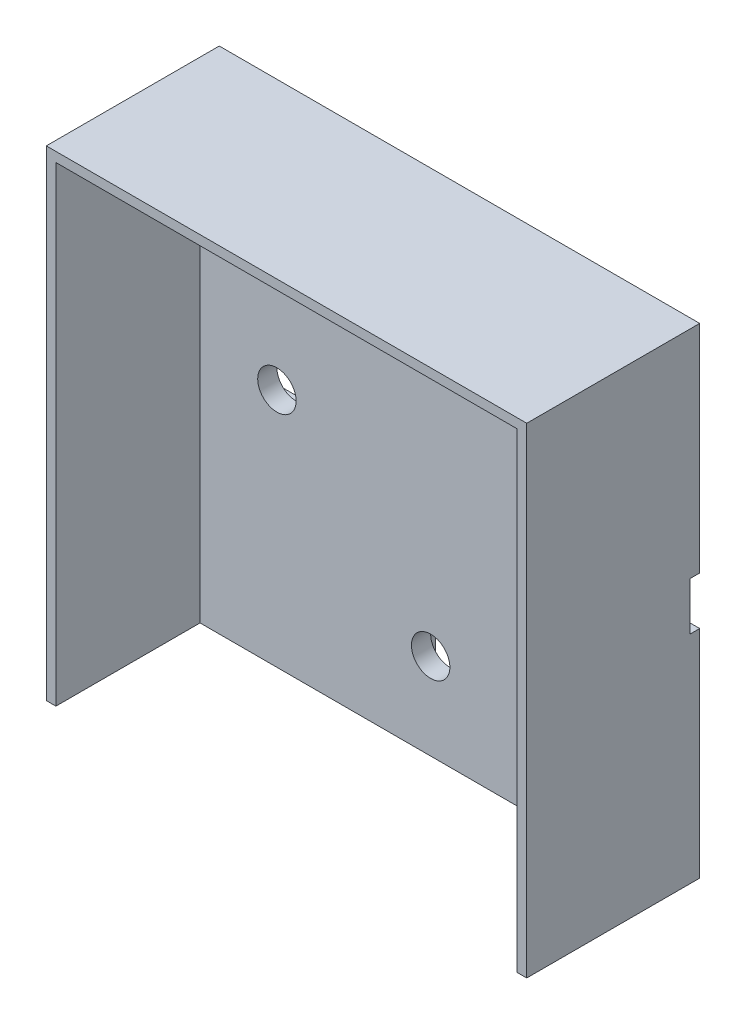
SolidWorks part; units mm, degrees
ref_plane "Přední rovina" through (0, 0, 0) normal (0, 0, 1) x (1, 0, 0)
ref_plane "Horní rovina" through (0, 0, 0) normal (0, 1, 0) x (1, 0, 0)
ref_plane "Pravá rovina" through (0, 0, 0) normal (1, 0, 0) x (0, 0, -1)
sketch "Skica1" plane through (0, 0, 0) normal (0, 0, 1) x (1, 0, 0)
  line L1 (25, 25) -> (-25, 25)
  line L2 (25, 25) -> (25, -25)
  line L3 (25, -25) -> (-25, -25)
  line L4 (-25, 25) -> (-25, -25)
  line L5 (25, 25) -> (-25, -25) construction
  line L6 (25, -25) -> (-25, 25) construction
  point P0 (0, 0)
  point P5 (-27.5, 0)
  point P11 (4.5, 0)
  dimension "D1" = 50
  dimension "D2" = 50
extrude "Přidat vysunutím2" add sketch "Skica1" along normal blind 3 contours L2 L1 L4 L3
sketch "Skica5" plane through (0, 0, 0) normal (0, 0, -1) x (-1, 0, 0)
  line L5 (-2.5, -2.5) -> (2.5, -2.5)
  line L10 (25, 25) -> (25, -25) construction
  line L11 (-25, 2.5) -> (25, 2.5)
  line L12 (-25, 2.5) -> (-25, -2.5)
  line L13 (-25, -2.5) -> (25, -2.5)
  line L14 (25, 2.5) -> (25, -2.5)
  line L15 (-25, 2.5) -> (25, -2.5) construction
  line L16 (-25, -2.5) -> (25, 2.5) construction
  line L17 (-2.5, -2.5) -> (-2.5, -25)
  line L18 (-2.5, -25) -> (2.5, -25)
  line L19 (2.5, -2.5) -> (2.5, -25)
  line L20 (-2.5, -2.5) -> (2.5, -25) construction
  line L21 (-2.5, -25) -> (2.5, -2.5) construction
  point P0 (0, 0)
  point P6 (0, -13.75)
  dimension "D1" = 5
  dimension "D2" = 22.5
  dimension "D3" = 5
  dimension "D4" = 0
extrude "Odebrat vysunutím3" cut sketch "Skica5" against normal blind 1 contours L11 L14 L13 L12 | L17 L5 L19 L18
sketch "Skica14" plane through (0, 0, 3) normal (0, 0, 1) x (1, 0, 0)
  line L1 (-25, 25) -> (25, 25)
  line L2 (-25, 25) -> (-25, -25)
  line L3 (-25, -25) -> (25, -25)
  line L4 (25, 25) -> (25, -25)
  line L5 (-24, 24) -> (24, 24)
  line L6 (-24, 24) -> (-24, -25)
  line L7 (-24, -25) -> (24, -25)
  line L8 (24, 24) -> (24, -25)
  line M13 (-25, -25) -> (25, -25)
  line M14 (25, -25) -> (25, 25)
  line M15 (25, 25) -> (-25, 25)
  line M16 (-25, 25) -> (-25, -25)
  dimension "D1" = 1
  dimension "D2" = 1
  dimension "D3" = 1
  dimension "D4" = 0
extrude "Přidat vysunutím9" add sketch "Skica14" along normal blind 15 contours L5 L8 L6 M13 M14 M15 M16
sketch "Skica17" plane through (0, 0, 1) normal (0, 0, -1) x (-1, 0, 0)
  line L0 (-25, 2.5) -> (-25, -2.5) construction
  line L1 (-10, -2.5) -> (-10, 2.5) construction
  line L2 (25, 2.5) -> (25, -2.5) construction
  line L3 (-2.5, -25) -> (2.5, -25) construction
  circle A0 centre (-16, 0) radius 2
  circle A1 centre (16, 0) radius 2
  circle A2 centre (0, -16) radius 2
  dimension "D1" = 4
  dimension "D2" = 4
  dimension "D6" = 4
  dimension "D3" = 9
  dimension "D4" = 6
  dimension "D5" = 9
  dimension "D7" = 9
extrude "Odebrat vysunutím8" cut sketch "Skica17" against normal blind 4
